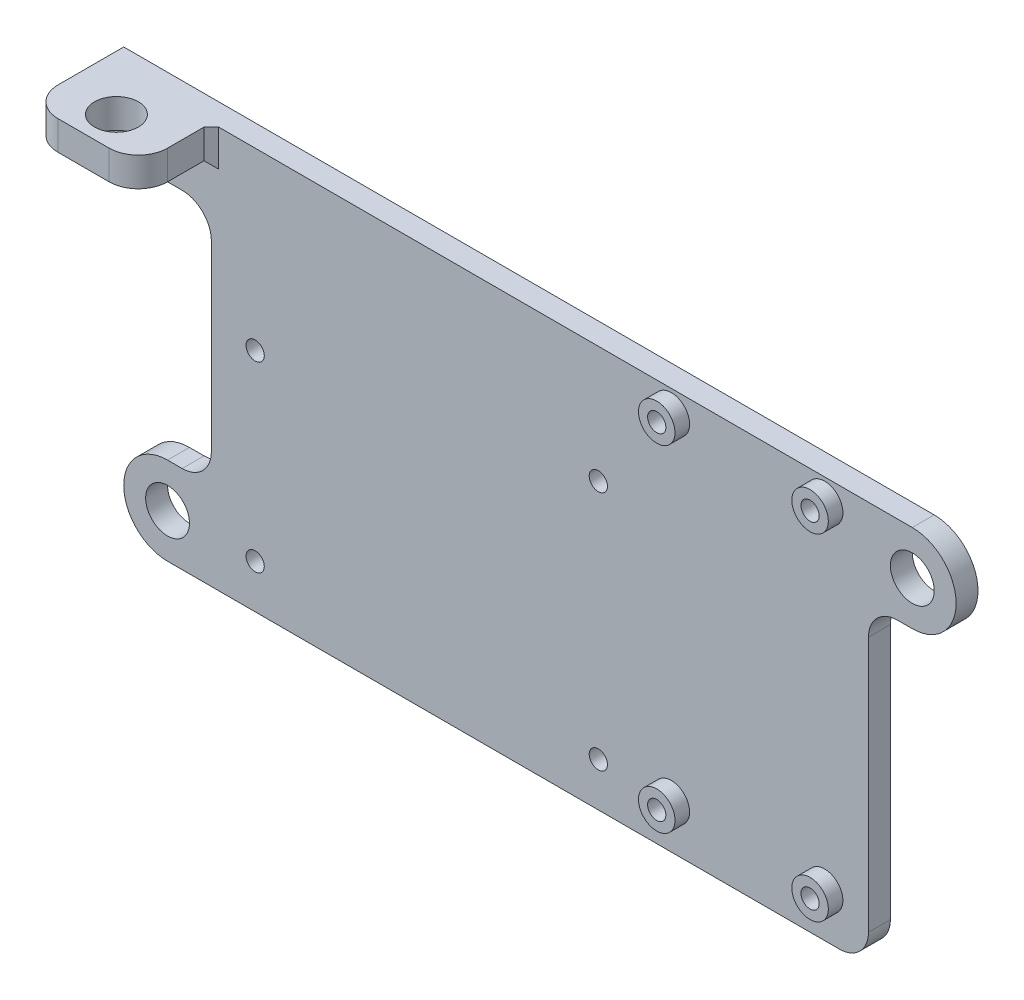
SolidWorks part; units mm, degrees
ref_plane "Спереди" through (0, 0, 0) normal (0, 0, 1) x (1, 0, 0)
ref_plane "Сверху" through (0, 0, 0) normal (0, 1, 0) x (1, 0, 0)
ref_plane "Справа" through (0, 0, 0) normal (1, 0, 0) x (0, 0, -1)
sketch "Эскиз1" plane through (0, 0, 0) normal (0, 0, 1) x (1, 0, 0)
  line L0 (53, 31) -> (53, 39) construction
  line L1 (0, 0) -> (90, 0)
  line L2 (0, 0) -> (0, 55)
  line L3 (0, 55) -> (90, 55)
  line L4 (90, 0) -> (90, 55)
  line L5 (6, 31) -> (53, 31) construction
  line L6 (6, 31) -> (6, 6) construction
  line L7 (6, 6) -> (53, 6) construction
  line L8 (53, 31) -> (53, 6) construction
  line L9 (84, 52) -> (63, 52) construction
  line L10 (84, 52) -> (84, 6) construction
  line L11 (84, 6) -> (63, 6) construction
  line L12 (63, 52) -> (63, 6) construction
  circle A0 centre (6, 31) radius 1.25
  circle A1 centre (6, 6) radius 1.25
  circle A2 centre (53, 39) radius 1.25
  circle A3 centre (53, 6) radius 1.25
  circle A4 centre (63, 6) radius 1.25
  circle A5 centre (63, 52) radius 1.25
  circle A6 centre (84, 52) radius 1.25
  circle A7 centre (84, 6) radius 1.25
  dimension "D11" = 2.5
  dimension "D1" = 25
  dimension "D2" = 47
  dimension "D3" = 33
  dimension "D4" = 10
  dimension "D5" = 21
  dimension "D6" = 46
  dimension "D7" = 6
  dimension "D8" = 6
  dimension "D9" = 6
  dimension "D10" = 6
extrude "Бобышка-Вытянуть1" add sketch "Эскиз1" along normal blind 3
sketch "Эскиз2" plane through (0, 0, 3) normal (0, 0, 1) x (1, 0, 0)
  line L0 (0, 55) -> (0, 0) construction
  line L1 (0, 55) -> (-15, 55)
  line L2 (0, 55) -> (0, 41)
  line L3 (-4, 45) -> (-15, 45)
  line L4 (-15, 55) -> (-15, 45)
  line L5 (0, 6) -> (-6, 6) construction
  line L6 (0, 0) -> (-6, 0)
  line L7 (-4, 12) -> (-6, 12)
  line L8 (90, 49) -> (96, 49) construction
  line L9 (90, 0) -> (90, 55) construction
  line L10 (90, 55) -> (96, 55)
  line L11 (94, 43) -> (96, 43)
  line L12 (90, 55) -> (0, 55) construction
  line L13 (0, 0) -> (0, 16)
  line L14 (90, 55) -> (90, 39)
  arc A0 (0, 41) -> (-4, 45) centre (-4, 41) ccw
  arc A2 (-6, 12) -> (-6, 0) centre (-6, 6) ccw
  arc A4 (96, 43) -> (96, 55) centre (96, 49) ccw
  circle A5 centre (-6, 6) radius 3
  circle A6 centre (96, 49) radius 3
  arc A7 (-4, 12) -> (0, 16) centre (-4, 16) ccw
  arc A8 (94, 43) -> (90, 39) centre (94, 39) ccw
  point P11 (-3, 6)
  point P16 (93, 49)
  dimension "D3" = 8
  dimension "D4" = 6
  dimension "D5" = 6
  dimension "D6" = 6
  dimension "D7" = 6
  dimension "D8" = 8
  dimension "D9" = 8
  dimension "D1" = 15
  dimension "D2" = 10
extrude "Бобышка-Вытянуть2" add sketch "Эскиз2" against normal blind 3
sketch "Эскиз3" plane through (0, 55, 0) normal (0, 1, 0) x (1, 0, 0)
  line L0 (-7.5, -3) -> (-7.5, -13) construction
  line L1 (-15, -3) -> (0, -3)
  line L2 (-15, -3) -> (-15, -13)
  line L3 (-15, -13) -> (0, -13)
  line L4 (0, -3) -> (0, -13)
  circle A0 centre (-7.5, -8.5) radius 3
  dimension "D2" = 6
  dimension "D1" = 10
  dimension "D3" = 15
  dimension "D4" = 4.5
extrude "Бобышка-Вытянуть3" add sketch "Эскиз3" against normal blind 4
chamfer "Фаска1" distance 1 angle 45 2 edges at (0, 53, 3) (-7.5, 51, 3)
sketch "Эскиз4" plane through (0, 0, 3) normal (0, 0, 1) x (1, 0, 0)
  circle A0 centre (63, 52) radius 2.5
  circle A1 centre (84, 52) radius 2.5
  circle A2 centre (63, 6) radius 2.5
  circle A3 centre (84, 6) radius 2.5
  circle A4 centre (63, 52) radius 1.25
  circle A5 centre (84, 52) radius 1.25
  circle A6 centre (63, 6) radius 1.25
  circle A7 centre (84, 6) radius 1.25
  dimension "D1" = 5
extrude "Бобышка-Вытянуть4" add sketch "Эскиз4" along normal blind 2
fillet "Скругление1" radius 4 4 edges at (-15, 53, 13) (0, 53, 13) (-15, 45, 1.5) (90, 0, 1.5)
